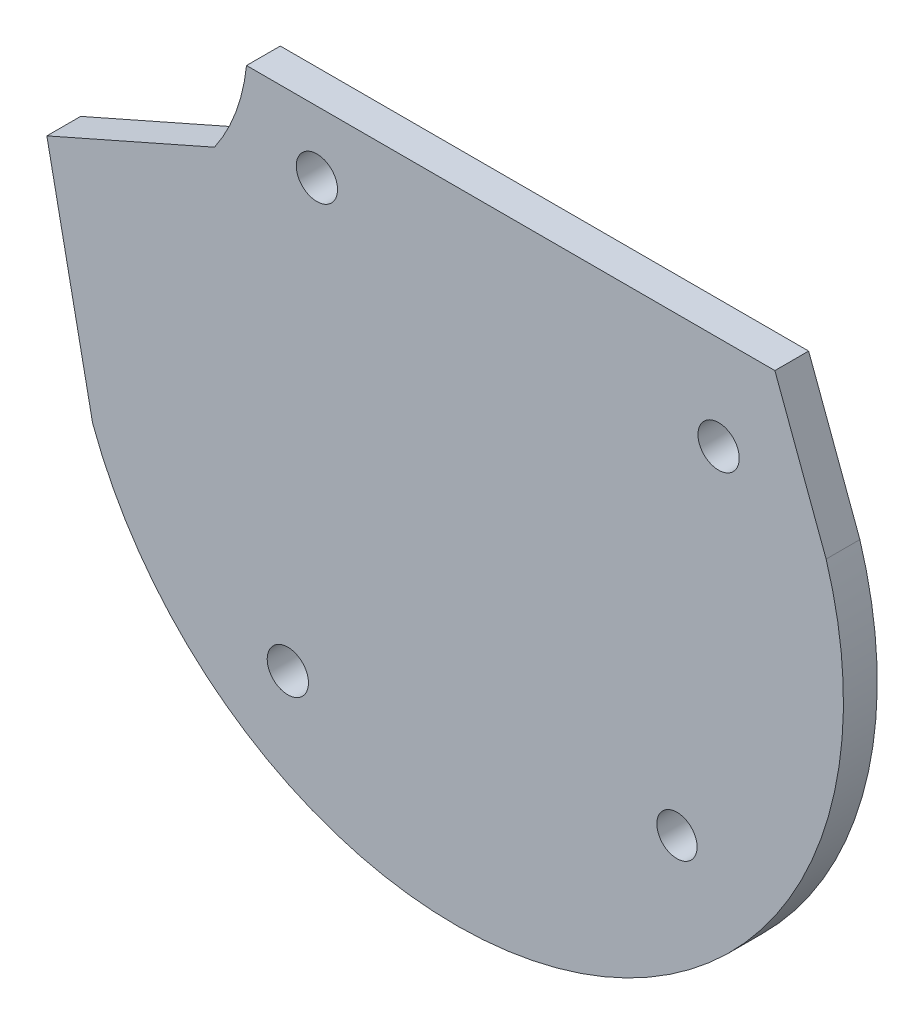
SolidWorks part; units mm, degrees
ref_plane "Front Plane" through (0, 0, 0) normal (0, 0, 1) x (1, 0, 0)
ref_plane "Top Plane" through (0, 0, 0) normal (0, 1, 0) x (1, 0, 0)
ref_plane "Right Plane" through (0, 0, 0) normal (1, 0, 0) x (0, 0, -1)
sketch "Sketch5" plane through (0, 0, 0) normal (0, 0, -1) x (-0.0184, 0.9998, 0)
  line L0 (33.8067, 26.1862) -> (34.4639, -9.5778)
  line L1 (28.6302, -11.8533) -> (23.8302, -23.2927)
  line L2 (23.8302, -23.2927) -> (8.4862, -20.4775)
  line L3 (33.8067, 26.1862) -> (24.4257, 29.4824)
  line L4 (30.1797, -4.8908) -> (34.3764, -4.8137) construction
  line L5 (34.3764, -4.8137) -> (34.4639, -9.5778) construction
  line L6 (34.4639, -9.5778) -> (34.3766, -9.5968) construction
  line L7 (27.5277, 22.2602) -> (33.8767, 22.3769) construction
  line L8 (27.5277, 22.2602) -> (27.4143, 28.4323) construction
  line L9 (3.3631, 18.996) -> (-4.6952, 18.8479) construction
  line L10 (3.3631, 18.996) -> (3.2246, 26.5341) construction
  line L11 (30.1797, -4.8908) -> (30.2892, -10.847) construction
  line L12 (0.3178, -7.4078) -> (0.4754, -15.9798) construction
  line L13 (0.3178, -7.4078) -> (-6.2927, -7.5293) construction
  arc A0 (34.4639, -9.5778) -> (28.6302, -11.8533) centre (36.0016, -22.1359) ccw
  arc A1 (24.4257, 29.4824) -> (8.4862, -20.4775) centre (17.1235, 4.2895) ccw
  circle A2 centre (27.5277, 22.2602) radius 1.397
  circle A3 centre (30.1797, -4.8908) radius 1.397
  circle A4 centre (3.3631, 18.996) radius 1.3622
  circle A5 centre (0.3178, -7.4078) radius 1.397
extrude "Extrude1" add sketch "Sketch5" along normal blind 2.286
